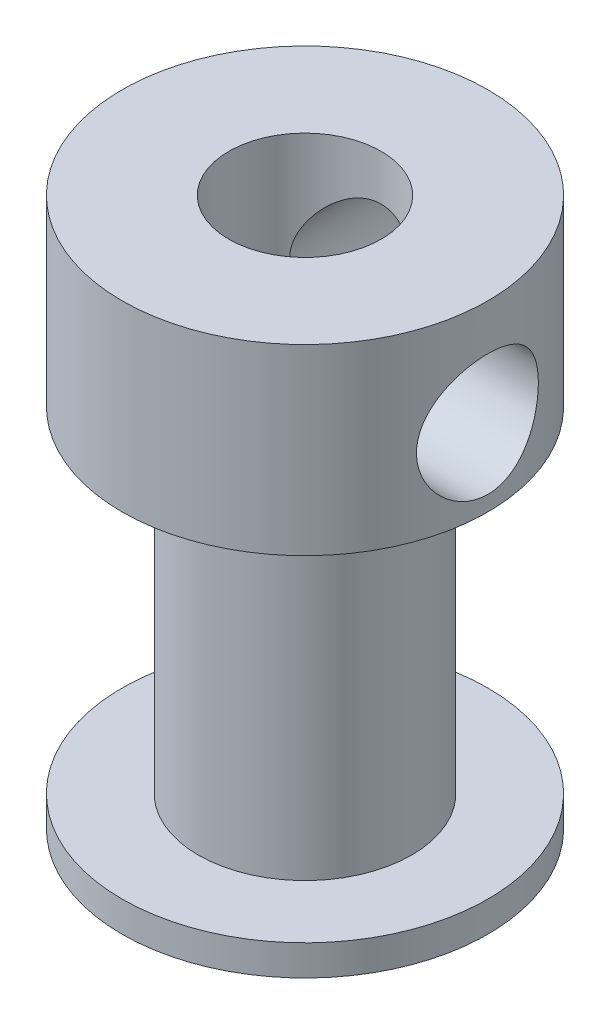
SolidWorks part; units mm, degrees
ref_plane "Front Plane" through (0, 0, 0) normal (0, 0, 1) x (1, 0, 0)
ref_plane "Top Plane" through (0, 0, 0) normal (0, 1, 0) x (1, 0, 0)
ref_plane "Right Plane" through (0, 0, 0) normal (1, 0, 0) x (0, 0, -1)
sketch "Sketch1" plane through (0, 0, 0) normal (0, 1, 0) x (1, 0, 0)
  circle A0 centre (0, 0) radius 6
  dimension "D1" = 12
extrude "Boss-Extrude1" add sketch "Sketch1" along normal blind 1
sketch "Sketch2" plane through (0, 1, 0) normal (0, 1, 0) x (1, 0, 0)
  circle A0 centre (0, 0) radius 3.5
  dimension "D1" = 7
extrude "Boss-Extrude2" add sketch "Sketch2" along normal blind 11
sketch "Sketch3" plane through (0, 12, 0) normal (0, 1, 0) x (1, 0, 0)
  circle A0 centre (0, 0) radius 6
  circle A1 centre (0, 0) radius 6 construction
extrude "Boss-Extrude3" add sketch "Sketch3" along normal blind 2
sketch "Sketch4" plane through (0, 14, 0) normal (0, 1, 0) x (1, 0, 0)
  circle A0 centre (0, 0) radius 6
  circle A1 centre (0, 0) radius 6 construction
extrude "Boss-Extrude4" add sketch "Sketch4" along normal blind 4
sketch "Sketch5" plane through (0, 18, 0) normal (0, 1, 0) x (1, 0, 0)
  circle A0 centre (0, 0) radius 2.5
  dimension "D1" = 5
extrude "Cut-Extrude1" cut sketch "Sketch5" against normal through all
sketch "Sketch6" plane through (0, 0, 0) normal (0, 0, 1) x (1, 0, 0)
  line L0 (6, 18) -> (-6, 18) construction
  circle A0 centre (0, 14.5) radius 2
  dimension "D1" = 4
  dimension "D2" = 3.5
extrude "Cut-Extrude2" cut sketch "Sketch6" against normal through all
pattern_circular "CirPattern1" count 2 every 90 about axis through (0, 14, 0) along (0, -1, 0) of "Cut-Extrude2"
